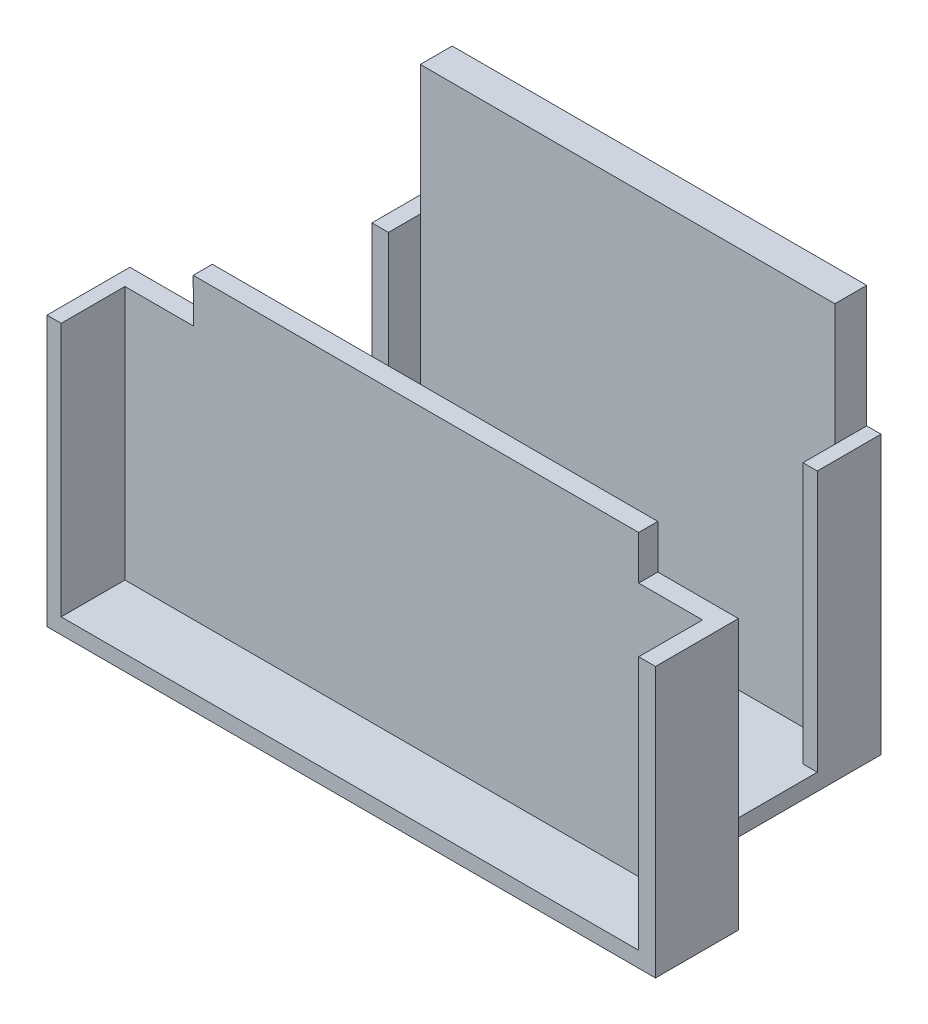
SolidWorks part; units mm, degrees
ref_plane "前视基准面" through (0, 0, 0) normal (0, 0, 1) x (1, 0, 0)
ref_plane "上视基准面" through (0, 0, 0) normal (0, 1, 0) x (1, 0, 0)
ref_plane "右视基准面" through (0, 0, 0) normal (1, 0, 0) x (0, 0, -1)
sketch "草图1" plane through (0, 0, 0) normal (0, 0, 1) x (1, 0, 0)
  line L1 (-19.0734, 43.3745) -> (45.9266, 43.3745)
  line L2 (-19.0734, 43.3745) -> (-19.0734, -16.6255)
  line L3 (-19.0734, -16.6255) -> (45.9266, -16.6255)
  line L4 (45.9266, 43.3745) -> (45.9266, -16.6255)
  line L6 (-19.0734, -16.6255) -> (-24.0734, -16.6255)
  line L7 (-19.0734, -16.6255) -> (-19.0734, 28.3745)
  line L8 (-19.0734, 28.3745) -> (-24.0734, 28.3745)
  line L9 (-24.0734, -16.6255) -> (-24.0734, 28.3745)
  line L11 (45.9266, -16.6255) -> (50.9266, -16.6255)
  line L12 (45.9266, -16.6255) -> (45.9266, 28.2299)
  line L13 (45.9266, 28.2299) -> (50.9266, 28.2299)
  line L14 (50.9266, -16.6255) -> (50.9266, 28.2299)
  line L16 (-24.0734, -16.6255) -> (50.9266, -16.6255)
  line L17 (-24.0734, -16.6255) -> (-24.0734, -20.7968)
  line L18 (-24.0734, -20.7968) -> (50.9266, -20.7968)
  line L19 (50.9266, -16.6255) -> (50.9266, -20.7968)
  line L20 (-24.0734, 28.3745) -> (-19.0734, 28.3745)
  line L21 (-24.0734, 28.3745) -> (-24.0734, -16.6255)
  line L22 (-24.0734, -16.6255) -> (-19.0734, -16.6255)
  line L23 (-19.0734, 28.3745) -> (-19.0734, -16.6255)
  dimension "D1" = 65
  dimension "D2" = 60
  dimension "D3" = 5
  dimension "D4" = 45
  dimension "D5" = 5
extrude "凸台-拉伸2" add sketch "草图1" along normal blind 5 contours L4 L1 L2 L3
sketch "草图2" plane through (0, 0, 0) normal (0, 0, -1) x (-1, 0, 0)
  line L0 (-45.9266, 24.2878) -> (-48.1691, 24.2878)
  line L1 (-45.9266, 43.3745) -> (-45.9266, -16.6255) construction
  line L2 (-48.1691, 24.2878) -> (-48.1691, -16.6255)
  line L3 (-48.1691, -16.6255) -> (-45.9266, -16.6255)
  line L4 (19.0734, -16.6255) -> (-45.9266, -16.6255) construction
  line L5 (-45.9266, 24.2878) -> (-45.9266, -16.6255)
extrude "凸台-拉伸3" add sketch "草图2" against normal blind 10
sketch "草图3" plane through (0, 0, 0) normal (0, 0, -1) x (-1, 0, 0)
  line L1 (19.0734, 23.0616) -> (21.6662, 23.0616)
  line L2 (19.0734, 43.3745) -> (19.0734, -16.6255) construction
  line L3 (21.6662, 23.0616) -> (21.6662, -16.6676)
  line L4 (21.6662, -16.6676) -> (19.0734, -16.6255)
  line L5 (19.0734, 23.0616) -> (19.0734, -16.6255)
extrude "凸台-拉伸4" add sketch "草图3" against normal blind 10
sketch "草图4" plane through (0, 0, 0) normal (0, 0, -1) x (-1, 0, 0)
  line L1 (-48.1691, -16.6255) -> (21.6791, -16.6255)
  line L2 (-48.1691, -16.6255) -> (-48.1691, -19.2457)
  line L3 (-48.1691, -19.2457) -> (21.6791, -19.2457)
  line L4 (21.6791, -16.6255) -> (21.6791, -19.2457)
extrude "凸台-拉伸6" add sketch "草图4" against normal blind 35
sketch "草图5" plane through (0, 0, 35) normal (0, 0, 1) x (1, 0, 0)
  line L0 (-21.6662, 23.0616) -> (-34.6138, 23.0616)
  line L1 (-21.6791, -19.2457) -> (48.1691, -19.2457)
  line L3 (-21.6791, 29.9376) -> (48.1691, 29.9376)
  line L5 (-34.6138, 23.0616) -> (-34.6138, -19.2457)
  line L6 (-34.6138, -19.2457) -> (-21.6791, -19.2457)
  line L7 (48.1691, -19.2457) -> (60.8041, -19.2457)
  line L8 (60.8041, -19.2457) -> (60.8041, 23.0616)
  line L9 (60.8041, 23.0616) -> (48.1691, 23.0616)
  line L10 (-21.6662, 23.0616) -> (-21.6791, 29.9376)
  line L11 (48.1691, 23.0616) -> (48.1691, 29.9376)
  dimension "D1" = 69.8482
  dimension "D2" = 49.1833
  dimension "D3" = 12.6349
  dimension "D4" = 42.3072
  dimension "D5" = 6.876
  dimension "D6" = 95.4178
  dimension "D7" = 89.892
extrude "凸台-拉伸7" add sketch "草图5" along normal blind 3 contours L1 L7 L8 L9 L11 L3 L10 L0 L5 L6
sketch "草图6" plane through (0, 0, 38) normal (0, 0, 1) x (1, 0, 0)
  line L0 (48.1691, 23.0616) -> (48.1691, 29.9376) construction
  line L1 (-21.6791, 29.9376) -> (48.1691, 29.9376)
  line L2 (-21.6791, 29.9376) -> (-21.6791, 27.1831)
  line L3 (-21.6791, 27.1831) -> (48.1691, 27.1831)
  line L4 (48.1691, 29.9376) -> (48.1691, 27.1831)
sketch "草图7" plane through (0, 0, 38) normal (0, 0, 1) x (1, 0, 0)
  line L0 (-34.6138, -19.2457) -> (60.8041, -19.2457) construction
  line L1 (-34.6138, 23.0616) -> (-32.3877, 23.0616)
  line L2 (-34.6138, 23.0616) -> (-34.6138, -19.2457)
  line L3 (-34.6138, -19.2457) -> (-32.3877, -19.2457)
  line L4 (-32.3877, 23.0616) -> (-32.3877, -19.2457)
  line L5 (60.8041, -19.2457) -> (60.8041, 23.0616) construction
  line L6 (-32.3877, -19.2457) -> (60.8041, -19.2457)
  line L7 (-32.3877, -19.2457) -> (-32.3877, -16.8033)
  line L8 (-32.3877, -16.8033) -> (60.8041, -16.8033)
  line L9 (60.8041, -19.2457) -> (60.8041, -16.8033)
  line L10 (60.8041, 23.0616) -> (48.1691, 23.0616) construction
  line L11 (60.8041, -16.8033) -> (58.1736, -16.8033)
  line L12 (60.8041, -16.8033) -> (60.8041, 23.0616)
  line L13 (60.8041, 23.0616) -> (58.1736, 23.0616)
  line L14 (58.1736, -16.8033) -> (58.1736, 23.0616)
  line M17 (-34.6138, -19.2457) -> (60.8041, -19.2457)
  line M18 (60.8041, -19.2457) -> (60.8041, 23.0616)
  line M19 (60.8041, 23.0616) -> (48.1691, 23.0616)
extrude "凸台-拉伸9" add sketch "草图7" along normal blind 10 contours L8 L4 M17 M18 | L14 L8 M18 M19
